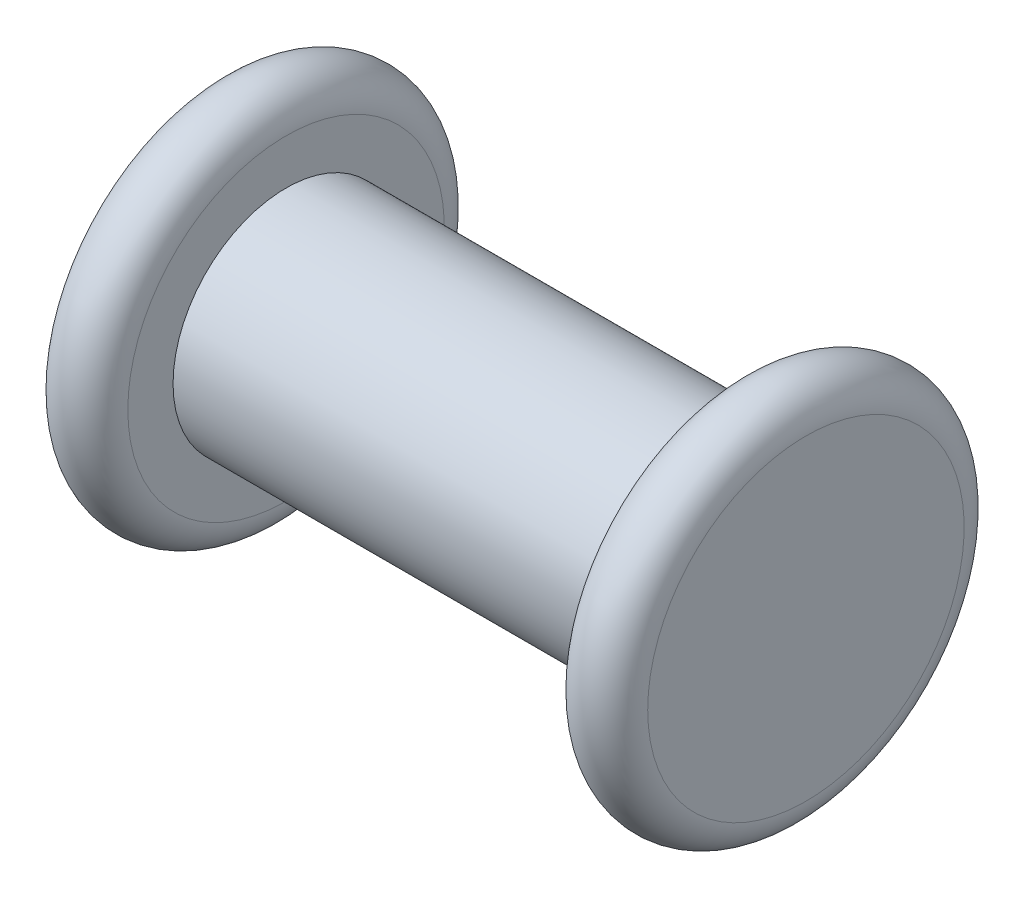
SolidWorks part; units mm, degrees
ref_plane "Front" through (0, 0, 0) normal (0, 0, 1) x (1, 0, 0)
ref_plane "Top" through (0, 0, 0) normal (0, 1, 0) x (1, 0, 0)
ref_plane "Right" through (0, 0, 0) normal (1, 0, 0) x (0, 0, -1)
sketch "Sketch1" plane through (0, 0, 0) normal (0, 0, 1) x (1, 0, 0)
  line L0 (-39.2428, 0) -> (42.5881, 0) construction
  line L1 (0, 17.9655) -> (0, -17.1174) construction
  line L2 (-8.255, 0) -> (-8.255, 4.445)
  line L3 (-6.35, 4.445) -> (-6.35, 3.175)
  line L4 (-6.35, 3.175) -> (6.35, 3.175)
  line L5 (-8.255, 0) -> (8.255, 0)
  line L6 (6.35, 4.445) -> (6.35, 3.175)
  line L7 (8.255, 0) -> (8.255, 4.445)
  arc A0 (-8.255, 4.445) -> (-6.35, 4.445) centre (-7.3025, 4.445) cw
  arc A1 (8.255, 4.445) -> (6.35, 4.445) centre (7.3025, 4.445) ccw
  point P13 (0, 0)
  point P14 (0, 3.175)
  dimension "D4" = 8.89
  dimension "D1" = 1.905
  dimension "D2" = 12.7
  dimension "D3" = 6.35
revolve "Base-Revolve" add sketch "Sketch1" angle 360 about L0
